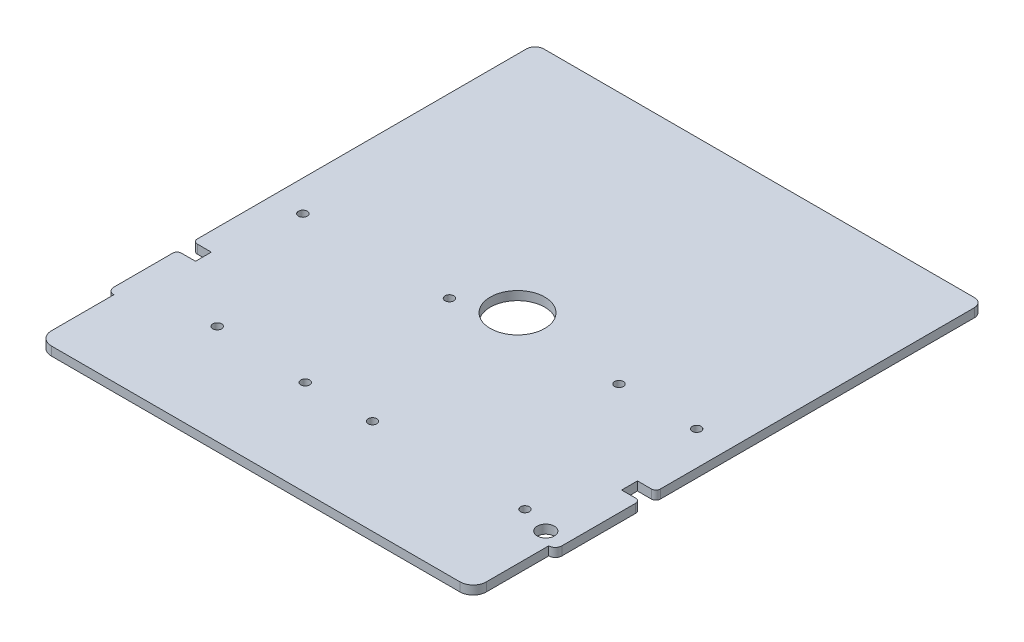
SolidWorks part; units mm, degrees
ref_plane "Front Plane" through (0, 0, 0) normal (0, 0, 1) x (1, 0, 0)
ref_plane "Top Plane" through (0, 0, 0) normal (0, 1, 0) x (1, 0, 0)
ref_plane "Right Plane" through (0, 0, 0) normal (1, 0, 0) x (0, 0, -1)
sketch "Sketch1" plane through (0, 0, 0) normal (0, 1, 0) x (1, 0, 0)
  line L0 (0, -1) -> (0, -21.45)
  line L1 (0.75, -22.2) -> (0.75, -29.3)
  line L2 (2.25, -30.8) -> (48.75, -30.8)
  line L3 (50.25, -29.3) -> (50.25, -22.2)
  line L4 (51, -21.45) -> (51, -1)
  line L5 (50, 0) -> (1, 0) construction
  line L6 (0, -1) -> (0, 25.5)
  line L7 (1, 26.5) -> (50, 26.5)
  line L8 (51, 25.5) -> (51, -1)
  arc A0 (0, -21.45) -> (0.75, -22.2) centre (0.75, -21.45) ccw
  arc A3 (50.25, -22.2) -> (51, -21.45) centre (50.25, -21.45) ccw
  arc A4 (51, -1) -> (50, 0) centre (50, -1) ccw construction
  arc A5 (1, 0) -> (0, -1) centre (1, -1) ccw construction
  arc A6 (48.75, -30.8) -> (50.25, -29.3) centre (48.75, -29.3) ccw
  arc A7 (0.75, -29.3) -> (2.25, -30.8) centre (2.25, -29.3) ccw
  arc A8 (50, 26.5) -> (51, 25.5) centre (50, 25.5) cw
  arc A9 (0, 25.5) -> (1, 26.5) centre (1, 25.5) cw
  point P19 (0.75, -30.8)
  dimension "D5" = 1.5
  dimension "D6" = 1
  dimension "D9" = 1
  dimension "D1" = 0.75
  dimension "D2" = 51
  dimension "D3" = 0.75
  dimension "D4" = 8.6
  dimension "D7" = 30.8
  dimension "D8" = 26.5
extrude "Boss-Extrude1" add sketch "Sketch1" along normal blind 1
sketch "Sketch2" plane through (0, 1, 0) normal (0, 1, 0) x (1, 0, 0)
  line L2 (0, -12.45) -> (2.1, -12.45)
  line L3 (0, 25.5) -> (0, -21.45) construction
  line L4 (2.1, -12.45) -> (2.1, -14.25)
  line L5 (2.1, -14.25) -> (0, -14.25)
  line L6 (0, -14.25) -> (0, -12.45)
  line L7 (51, -10.75) -> (48.9, -10.75)
  line L8 (51, -21.45) -> (51, 25.5) construction
  line L9 (48.9, -10.75) -> (48.9, -12.55)
  line L10 (48.9, -12.55) -> (51, -12.55)
  line L11 (51, -12.55) -> (51, -10.75)
  arc A1 (28.6, -1) -> (22.4, -1) centre (25.5, -1) cw
  arc A2 (22.4, -1) -> (28.6, -1) centre (25.5, -1) cw
  dimension "D2" = 1
  dimension "D10" = 3.1
  dimension "D1" = 6.2
  dimension "D3" = 25.5
  dimension "D4" = 12.45
  dimension "D5" = 10.75
  dimension "D6" = 1.8
  dimension "D7" = 1.8
  dimension "D8" = 2.1
  dimension "D9" = 2.1
extrude "Cut-Extrude1" cut sketch "Sketch2" against normal through all both and the other way through all
fillet "Fillet1" radius 0.5 4 edges at (0, 0.5, 14.25) (0, 0.5, 12.45) (51, 0.5, 10.75) (51, 0.5, 12.55)
sketch "Sketch3" plane through (0, 1, 0) normal (0, 1, 0) x (1, 0, 0)
  line L0 (0.75, -22.2) -> (0.75, -29.3) construction
  line L1 (2.25, -30.8) -> (48.75, -30.8) construction
  line L2 (51, -21.45) -> (51, -13.05) construction
  line L3 (0, 25.5) -> (0, -11.95) construction
  line L5 (51, -10.25) -> (51, 25.5) construction
  circle A0 centre (3.52, -3.45) radius 0.5
  circle A1 centre (20.2, -3.45) radius 0.5
  circle A2 centre (38.3, -2.25) radius 0.5
  circle A3 centre (47.14, -2.25) radius 0.5
  circle A4 centre (45.29, -19.95) radius 0.5
  circle A5 centre (27.94, -19.95) radius 0.5
  circle A6 centre (20.29, -19.95) radius 0.5
  circle A7 centre (9.75, -19.43) radius 0.5
  circle A8 centre (48.627, -20.91) radius 0.975
  dimension "D1" = 1
  dimension "D9" = 1.95
  dimension "D2" = 9
  dimension "D3" = 10.54
  dimension "D4" = 7.65
  dimension "D5" = 17.35
  dimension "D6" = 9.89
  dimension "D7" = 2.373
  dimension "D8" = 10.85
  dimension "D10" = 11.37
  dimension "D11" = 3.52
  dimension "D12" = 3.86
  dimension "D13" = 20.2
  dimension "D14" = 3.45
  dimension "D15" = 12.7
  dimension "D16" = 2.25
extrude "Cut-Extrude2" cut sketch "Sketch3" against normal through all both contours A0 | A1 | A2 | A3 | A8 | A4 | A5 | A6 | A7
